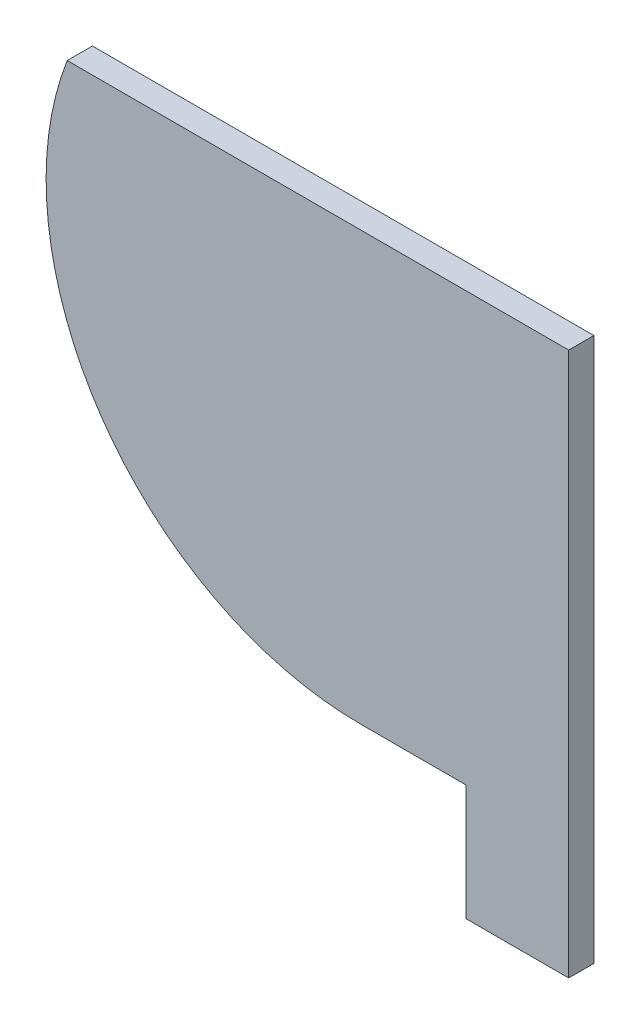
SolidWorks part; units mm, degrees
ref_plane "Front Plane" through (0, 0, 0) normal (0, 0, 1) x (1, 0, 0)
ref_plane "Top Plane" through (0, 0, 0) normal (0, 1, 0) x (1, 0, 0)
ref_plane "Right Plane" through (0, 0, 0) normal (1, 0, 0) x (0, 0, -1)
sketch "Sketch1" plane through (0, 0, 0) normal (0, 0, 1) x (1, 0, 0)
  line L12 (0, 0) -> (0, -85)
  line L13 (-41.2806, -85) -> (0, -85)
  line L14 (0, 0) -> (-99.5901, 0)
  arc A3 (-99.5901, 0) -> (-41.2806, -85) centre (-41.2806, -22.5) ccw
  dimension "D1" = 62.5
  dimension "D2" = 41.2806
  dimension "D3" = 85
extrude "Boss-Extrude1" add sketch "Sketch1" along normal blind 5
sketch "Sketch2" plane through (0, 0, 5) normal (0, 0, 1) x (1, 0, 0)
  line L0 (-20.3802, -85) -> (-20.3802, -108)
  line L1 (-20.3802, -85) -> (0, -85)
  line L2 (-20.3802, -108) -> (0, -108)
  line L3 (0, -85) -> (0, -108)
  line L5 (-3.1602, -108) -> (-24.6602, -108) construction
  line L8 (-41.2806, -85) -> (0, -85) construction
  line L12 (-2.1602, -87.011) -> (-2.1602, -110.6927) construction
  line L13 (-2.1602, -108) -> (-2.1602, -103) construction
  line L14 (-21.3802, -88.5135) -> (-21.3802, -110.6927) construction
  line L15 (-21.3802, -103) -> (-21.3802, -108) construction
  line L17 (0, -85) -> (0, 0) construction
  dimension "D1" = 1
extrude "Boss-Extrude2" add sketch "Sketch2" against normal blind 5
